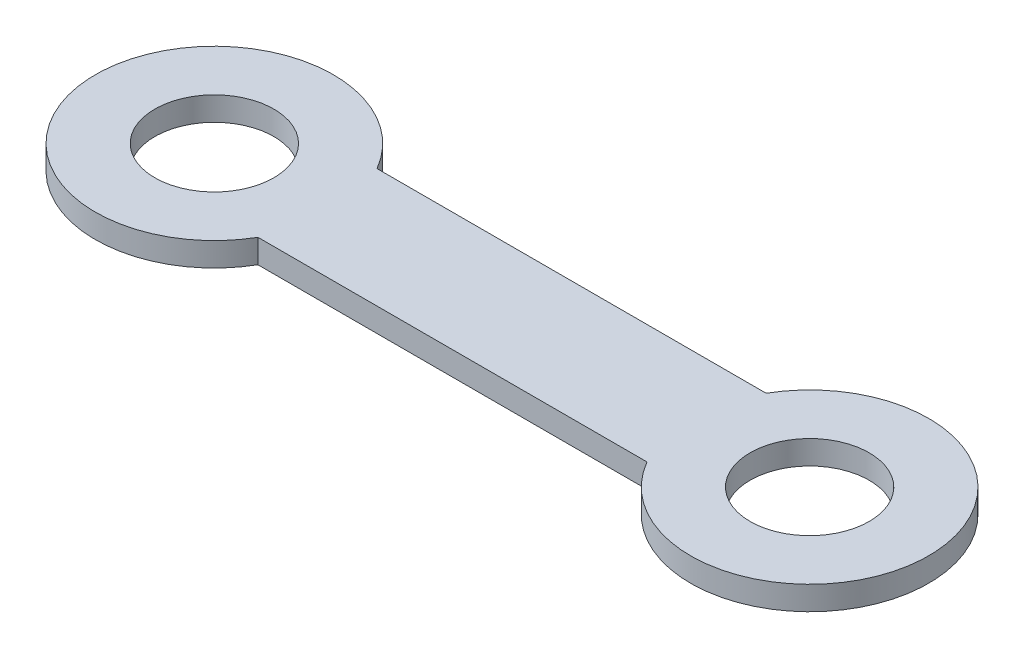
SolidWorks part; units mm, degrees
ref_plane "前基準面" through (0, 0, 0) normal (0, 0, 1) x (1, 0, 0)
ref_plane "上基準面" through (0, 0, 0) normal (0, 1, 0) x (1, 0, 0)
ref_plane "右基準面" through (0, 0, 0) normal (1, 0, 0) x (0, 0, -1)
sketch "草圖5" plane through (0, 0, 0) normal (0, 1, 0) x (1, 0, 0)
  line L0 (8.6603, -5) -> (41.3397, -5)
  line L2 (41.3397, 5) -> (8.6603, 5)
  circle A0 centre (0, 0) radius 5
  arc A1 (8.6603, 5) -> (8.6603, -5) centre (0, 0) ccw
  arc A2 (41.3397, -5) -> (41.3397, 5) centre (50, 0) ccw
  circle A3 centre (50, 0) radius 5
  point P3 (153.6886, 5)
  point P5 (0, 0)
  point P10 (134.7238, 0)
  dimension "D1" = 10
  dimension "D2" = 10
  dimension "D3" = 10
  dimension "D4" = 50
extrude "填料-伸長1" add sketch "草圖5" along normal blind 2
